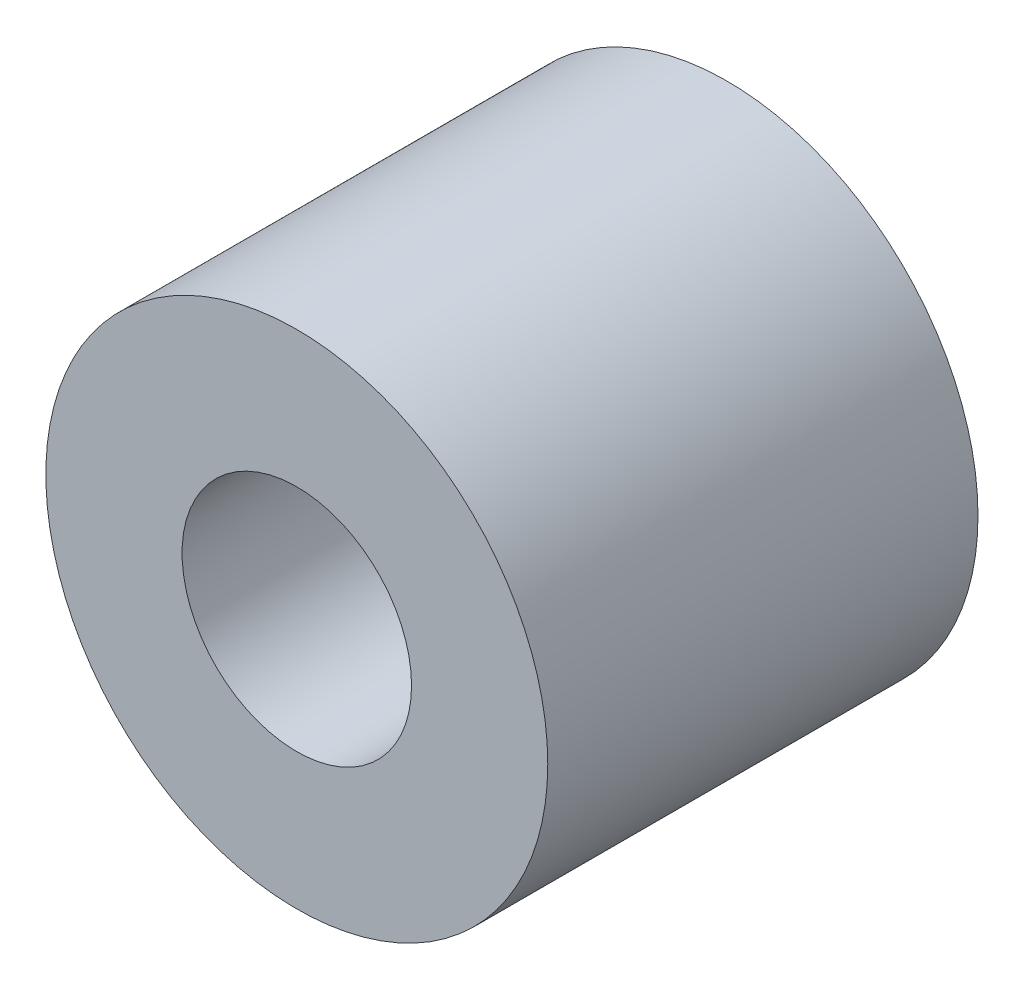
SolidWorks part; units mm, degrees
ref_plane "Alzado" through (0, 0, 0) normal (0, 0, 1) x (1, 0, 0)
ref_plane "Planta" through (0, 0, 0) normal (0, 1, 0) x (1, 0, 0)
ref_plane "Vista lateral" through (0, 0, 0) normal (1, 0, 0) x (0, 0, -1)
sketch "Croquis1" plane through (0, 0, 0) normal (0, 0, 1) x (1, 0, 0)
  circle A0 centre (0, 0) radius 3.5
  circle A1 centre (0, 0) radius 1.6
extrude "Saliente-Extruir1" add sketch "Croquis1" along normal blind 6
